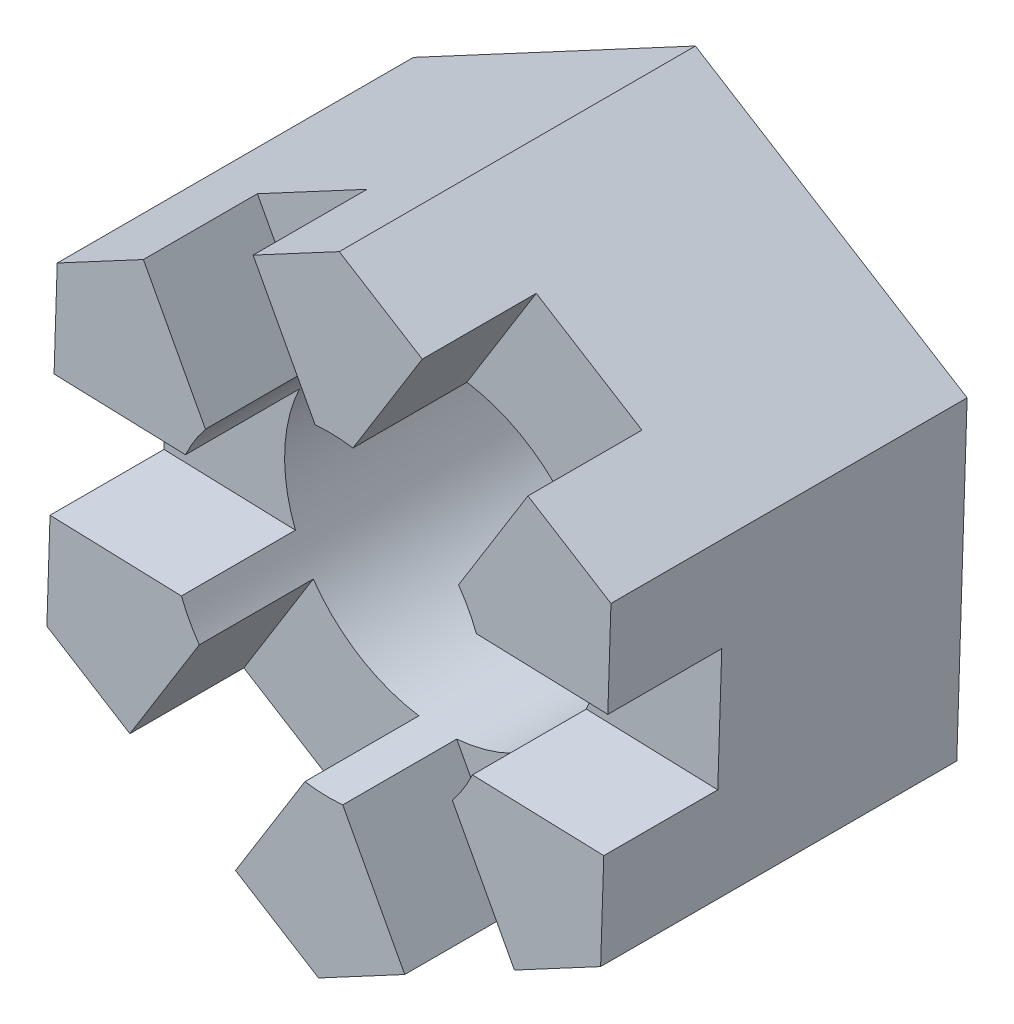
SolidWorks part; units mm, degrees
ref_plane "Front Plane" through (0, 0, 0) normal (0, 0, 1) x (1, 0, 0)
ref_plane "Top Plane" through (0, 0, 0) normal (0, 1, 0) x (1, 0, 0)
ref_plane "Right Plane" through (0, 0, 0) normal (1, 0, 0) x (0, 0, -1)
sketch "Sketch1" plane through (0, 0, 0) normal (0, 0, 1) x (1, 0, 0)
  line L1 (5.6572, 3.0263) -> (0.2077, 6.4124)
  line L2 (0.2077, 6.4124) -> (-5.4495, 3.3861)
  line L3 (-5.4495, 3.3861) -> (-5.6572, -3.0263)
  line L4 (-5.6572, -3.0263) -> (-0.2077, -6.4124)
  line L5 (-0.2077, -6.4124) -> (5.4495, -3.3861)
  line L6 (5.4495, -3.3861) -> (5.6572, 3.0263)
  circle A0 centre (0, 0) radius 5.5562 construction
  circle A1 centre (0, 0) radius 3.175
extrude "Extrude1" add sketch "Sketch1" along normal blind 7.1437
sketch "Sketch2" plane through (0, 0, 7.1437) normal (0, 0, 1) x (1, 0, 0)
  line L0 (-4.4109, -4.7353) -> (2.2919, 6.0519)
  line L1 (-4.4109, -4.7353) -> (-2.2919, -6.0519)
  line L2 (2.2919, 6.0519) -> (4.4109, 4.7353)
  line L3 (-2.2919, -6.0519) -> (4.4109, 4.7353)
  line L4 (-4.4109, -4.7353) -> (4.4109, 4.7353) construction
  line L5 (2.2919, 6.0519) -> (-2.2919, -6.0519) construction
  point P1 (0, 0)
extrude "Extrude2" cut sketch "Sketch2" against normal blind 2.286
pattern_circular "CirPattern1" count 3 over 360 about axis through (0, 0, 0) along (0, 0, 1) of "Extrude2"
